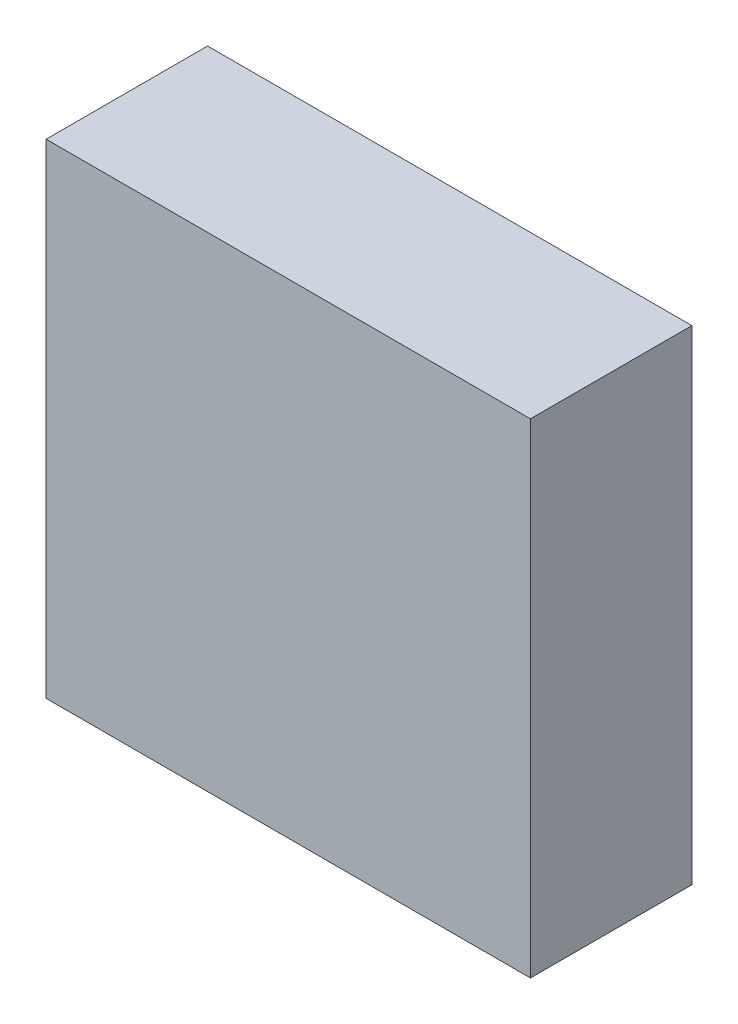
SolidWorks part; units mm, degrees
ref_plane "Спереди" through (0, 0, 0) normal (0, 0, 1) x (1, 0, 0)
ref_plane "Сверху" through (0, 0, 0) normal (0, 1, 0) x (1, 0, 0)
ref_plane "Справа" through (0, 0, 0) normal (1, 0, 0) x (0, 0, -1)
sketch "Эскиз1" plane through (0, 0, 0) normal (0, 0, 1) x (1, 0, 0)
  line L0 (-2.591, 2.6036) -> (2.209, 2.6036)
  line L1 (-2.591, 2.6036) -> (-2.591, -2.1964)
  line L2 (-2.591, -2.1964) -> (2.209, -2.1964)
  line L3 (2.209, 2.6036) -> (2.209, -2.1964)
  line L4 (-2.591, 2.6036) -> (2.209, -2.1964) construction
  line L5 (-2.591, -2.1964) -> (2.209, 2.6036) construction
  point P0 (-0.191, 0.2036)
  dimension "D1" = 4.8
  dimension "D2" = 4.8
extrude "Бобышка-Вытянуть1" add sketch "Эскиз1" along normal blind 1.6
